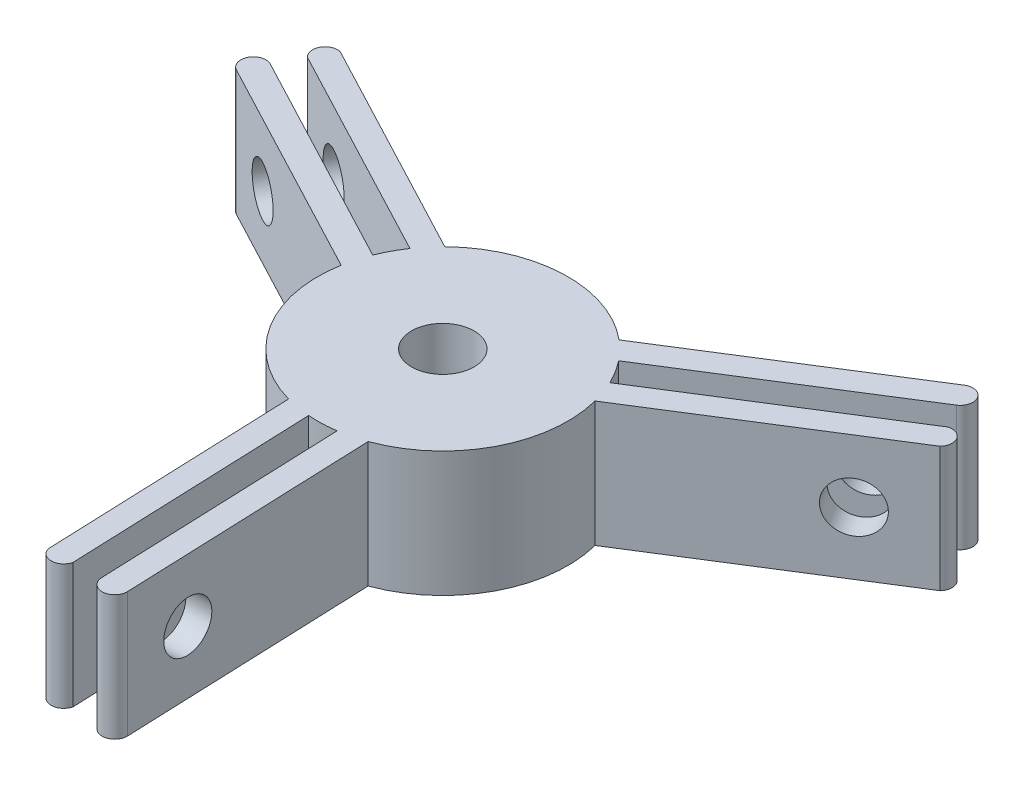
SolidWorks part; units mm, degrees
ref_plane "Front Plane" through (0, 0, 0) normal (0, 0, 1) x (1, 0, 0)
ref_plane "Top Plane" through (0, 0, 0) normal (0, 1, 0) x (1, 0, 0)
ref_plane "Right Plane" through (0, 0, 0) normal (1, 0, 0) x (0, 0, -1)
sketch "Sketch1" plane through (0, 0, 0) normal (0, 1, 0) x (1, 0, 0)
  line L0 (0, 0) -> (2.1154, 1.3323) construction
  line L1 (3.4294, -9.3936) -> (4.1979, -29.3788)
  line L2 (6.4203, 7.6668) -> (23.3438, 18.3249)
  line L3 (7.8455, 6.2007) -> (24.4096, 16.6325)
  line L4 (1.4472, -9.8947) -> (2.1994, -29.4556)
  line L5 (9.6881, 2.4781) -> (26.6116, 13.1362)
  line L6 (9.0115, 4.3351) -> (25.582, 14.7709)
  line L7 (-0.7514, -9.9717) -> (0.001, -29.5402)
  line L8 (-2.698, -9.6292) -> (-1.9295, -29.6144)
  line L9 (-9.8498, 1.7268) -> (-27.5417, 11.0539)
  line L10 (-9.2927, 3.694) -> (-26.609, 12.8231)
  line L11 (-8.2601, 5.6366) -> (-25.583, 14.7692)
  line L12 (-6.9901, 7.1511) -> (-24.6821, 16.4782)
  arc A0 (6.4203, 7.6668) -> (-6.9901, 7.1511) centre (0, 0) ccw
  circle A1 centre (0, 0) radius 2.5
  arc A2 (2.1994, -29.4556) -> (4.1979, -29.3788) centre (3.1986, -29.4172) ccw
  arc A3 (24.4096, 16.6325) -> (23.3438, 18.3249) centre (23.8767, 17.4787) ccw
  arc A4 (0.001, -29.5402) -> (-1.9295, -29.6144) centre (-0.9742, -29.3189) cw
  arc A5 (25.582, 14.7709) -> (26.6116, 13.1362) centre (25.878, 13.8157) cw
  arc A6 (9.0115, 4.3351) -> (7.8455, 6.2007) centre (0, 0) ccw
  arc A7 (-26.609, 12.8231) -> (-27.5417, 11.0539) centre (-27.0754, 11.9385) ccw
  arc A8 (-25.583, 14.7692) -> (-24.6821, 16.4782) centre (-24.9038, 15.5031) cw
  arc A9 (-9.8498, 1.7268) -> (-2.698, -9.6292) centre (0, 0) ccw
  arc A10 (-8.2601, 5.6366) -> (-9.2927, 3.694) centre (0, 0) ccw
  arc A11 (-0.7514, -9.9717) -> (1.4472, -9.8947) centre (0, 0) ccw
  arc A12 (3.4294, -9.3936) -> (9.6881, 2.4781) centre (0, 0) ccw
  point P7 (15.6157, 12.3163)
  point P15 (17.8539, 8.7623)
  point P39 (0, 0)
  dimension "D1" = 20
  dimension "D2" = 5
  dimension "D3" = 2
  dimension "D4" = 20
  dimension "D5" = 2.2
  dimension "D6" = 3
extrude "Boss-Extrude1" add sketch "Sketch1" along normal blind 10
sketch "Sketch2" plane through (3.0637, 0, -0.1178) normal (0.9993, 0, -0.0384) x (-0.0384, 0, -0.9993)
  line L0 (-29.5184, 10) -> (-29.5184, 0) construction
  line L1 (-29.5184, 0) -> (-9.5184, 0) construction
  circle A0 centre (-24.5184, 5) radius 2
  dimension "D1" = 5
  dimension "D3" = 4
  dimension "D2" = 5
extrude "Cut-Extrude1" cut sketch "Sketch2" against normal blind 10
pattern_circular "CirPattern1" count 3 over 360 about axis through (0, 10, 0) along (0, -1, 0) of "Cut-Extrude1"
